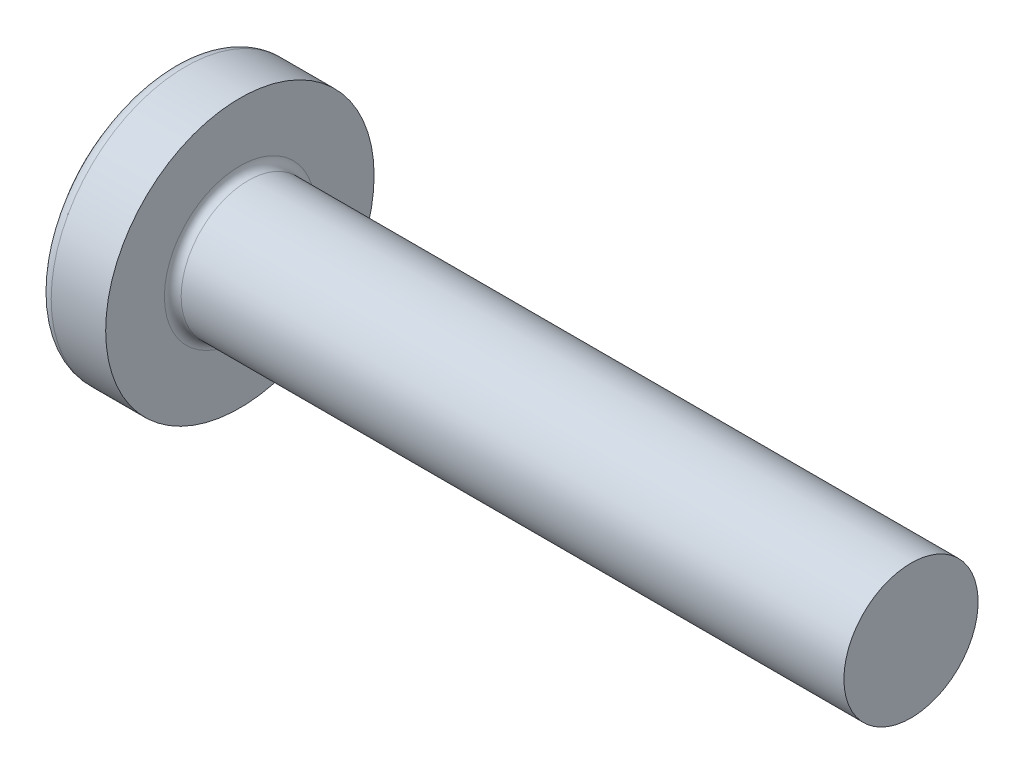
SolidWorks part; units mm, degrees
ref_plane "Plane1" through (0, 0, 0) normal (0, 0, 1) x (1, 0, 0)
ref_plane "Plane2" through (0, 0, 0) normal (0, 1, 0) x (1, 0, 0)
ref_plane "Plane3" through (0, 0, 0) normal (1, 0, 0) x (0, 0, -1)
sketch "BodySke" plane through (0, 0, 0) normal (0, 0, 1) x (1, 0, 0)
  line L0 (1.3, 0.8) -> (1.3, 1.6)
  line L1 (1.475, 6.35) -> (1.475, -3.175) construction
  line L2 (-25.4, 0) -> (127, 0) construction
  line L3 (9.3, 0) -> (0, 0)
  line L4 (1.3, 0.8) -> (9.3, 0.8)
  line L5 (9.3, 0.8) -> (9.3, 0)
  line L6 (0.6507, 1.6) -> (1.3, 1.6)
  line L8 (1.3, 6.35) -> (1.3, -3.175) construction
  arc A0 (0.5326, 1.5426) -> (0, 0) centre (2.5, 0) ccw
  arc A2 (0.5326, 1.5426) -> (0.6507, 1.6) centre (0.6507, 1.45) cw
  dimension "Head_crown_rad" = 2.5
  dimension "Head_fillet_rad" = 0.15
  dimension "Head_ht" = 1.3
  dimension "Head_dia" = 3.2
  dimension "Advance" = 0.35
  dimension "Diameter" = 1.6
revolve "Base-Revolve" add sketch "BodySke"
cosmetic thread "ThreadCosmetic" [suppressed]
fillet "Fillet1" radius 0.1 1 edges at (1.3, 0, 0.8)
sketch "Sketch3" plane through (0, 0, 0) normal (1, 0, 0) x (0, 0, -1)
  line L0 (0.24, -0.8) -> (-0.24, -0.8)
  line L1 (0.24, -0.8) -> (0.24, 0.8)
  line L2 (-0.24, 0.8) -> (0.24, 0.8)
  line L3 (-0.24, 0.8) -> (-0.24, -0.8)
  dimension "Cross_dia" = 1.6
  dimension "D1" = 0.8
  dimension "Cross_width" = 0.48
  dimension "D2" = 0.24
ref_plane "Plane4" through (0.9, 0, 0) normal (1, 0, 0) x (0, 0, -1)
sketch "Sketch4" plane through (0.9, 0, 0) normal (1, 0, 0) x (0, 0, -1)
  line L0 (0.24, -0.3513) -> (-0.24, -0.3513)
  line L1 (0.24, -0.3513) -> (0.24, 0.3513)
  line L2 (-0.24, 0.3513) -> (0.24, 0.3513)
  line L3 (-0.24, 0.3513) -> (-0.24, -0.3513)
  dimension "D1" = 0.48
  dimension "D2" = 0.7026
  dimension "D3" = 0.24
  dimension "D4" = 0.3513
loft "Recess" cut profiles "Sketch3", "Sketch4"
pattern_circular "RecPat" count 2 every 90 about axis through (0, 0, 0) along (1, 0, 0) of "Recess"
sketch "RecCorSke" plane through (0, 0, 0) normal (0, 0, 1) x (1, 0, 0)
  line L0 (-3.175, 0) -> (15.875, 0) construction
  line L1 (-25.4, 0) -> (127, 0) construction
  line L2 (0, 0) -> (0, 0.4184)
  line L3 (0, 0.4184) -> (0.9, 0.3555)
  line L4 (0.9, 0.3555) -> (1.0155, 0)
  line L5 (1.0155, 0) -> (0, 0)
  dimension "Diameter" = 0.711
  dimension "Depth" = 0.9
  dimension "Draft_angle" = 4
  dimension "Bottom_angle" = 18
revolve "RecessCore" cut sketch "RecCorSke" angle 360 about L0
sketch "ThdSchSke" plane through (0, 0, 0) normal (0, 0, 1) x (1, 0, 0)
  line L0 (2, -0.601) -> (1.8607, -0.8)
  line L1 (2, -0.601) -> (2.1393, -0.8)
  line L2 (2.1393, -0.8) -> (2.1393, -1)
  line L3 (-3.175, 0) -> (5.1513, 0) construction
  line L5 (2.1393, -1) -> (1.8607, -1)
  line L6 (1.8607, -1) -> (1.8607, -0.8)
  dimension "Diameter" = 1.6
  dimension "SideAngle" = 55
  dimension "VeeAngle" = 70
  dimension "Thread_minor" = 1.202
  dimension "Overcut" = 2
  dimension "Start" = 2
revolve "ThreadSchematic" [suppressed] cut sketch "ThdSchSke" angle 360 about L3
pattern_linear "ThdSchPat" [suppressed]
equation "\"D1@Sketch3\" = \"Cross_dia@Sketch3\" / 2"
equation "\"D2@Sketch3\" = \"Cross_width@Sketch3\" / 2"
equation "\"Depth@RecCorSke\" = \"Cross_depth@Plane4\""
equation "\"D1@Sketch4\" = \"Cross_width@Sketch3\""
equation "\"D2@Sketch4\" = \"Cross_dia@Sketch3\" - 2.0 * \"Cross_depth@Plane4\" * tan(26.5  * 0.017453292)"
equation "\"D3@Sketch4\" = \"D1@Sketch4\" / 2"
equation "\"D4@Sketch4\" = \"D2@Sketch4\" / 2"
equation "\"Thread_length@ThreadCosmetic\" = ((sgn( (\"Length@BodySke\" - \"Advance@BodySke\" * 2.0 ) - \"Thread_nom@BodySke\" )-1)*( (\"Length@BodySke\" - \"Advance@BodySke\" * 2.0 ) - \"Thread_nom@BodySke\" ))/-2+ \"Thread_nom@BodySke\""
equation "\"Thread_minor@ThdSchSke\" = \"Thread_minor@ThreadCosmetic\""
equation "\"Diameter@ThdSchSke\" = \"Diameter@BodySke\""
equation "\"Overcut@ThdSchSke\" = \"Diameter@BodySke\" * 1.25"
equation "\"Start@ThdSchSke\" = \"Head_ht@BodySke\" + \"Length@BodySke\" - \"Thread_length@ThreadCosmetic\"  '---Non-countersunk---"
equation "\"Num_threads@ThdSchPat\" = int( \"Thread_length@ThreadCosmetic\" / \"Advance@BodySke\" + 0.999 )  + 1"
equation "\"Advance@ThdSchPat\" = \"Thread_length@ThreadCosmetic\" /  (\"Num_threads@ThdSchPat\" - 1) 'relax it"
